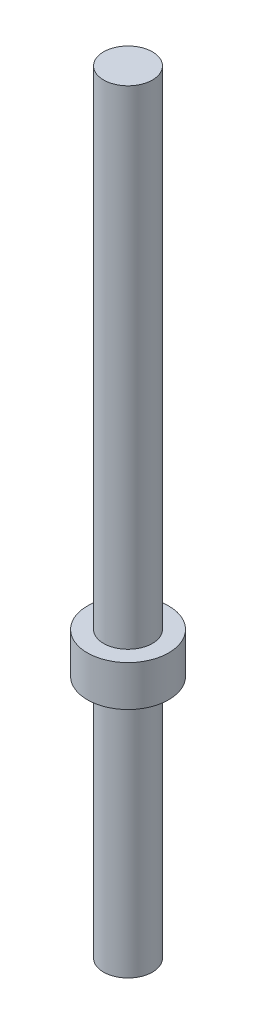
SolidWorks part; units mm, degrees
ref_plane "Front Plane" through (0, 0, 0) normal (0, 0, 1) x (1, 0, 0)
ref_plane "Top Plane" through (0, 0, 0) normal (0, 1, 0) x (1, 0, 0)
ref_plane "Right Plane" through (0, 0, 0) normal (1, 0, 0) x (0, 0, -1)
sketch "Sketch2" plane through (0, 0, 0) normal (0, 1, 0) x (1, 0, 0)
  circle A0 centre (0, 0) radius 0.3
  dimension "D1" = 0.6
extrude "Base-Extrude" add sketch "Sketch2" along normal blind 6.5
sketch "Sketch3" plane through (0, 0, 0) normal (0, -1, 0) x (1, 0, 0)
  circle A0 centre (0, 0) radius 0.5
  circle A1 centre (0, 0) radius 0.3 construction
  dimension "D1" = 1
extrude "Boss-Extrude1" add sketch "Sketch3" against normal blind 0.5
sketch "Sketch4" plane through (0, 0, 0) normal (0, -1, 0) x (1, 0, 0)
  circle A0 centre (0, 0) radius 0.3
  circle A1 centre (0, 0) radius 0.3 construction
extrude "Boss-Extrude2" add sketch "Sketch4" along normal blind 3
ref_plane "Board Plane" through (0, -3, 0) normal (0, 1, 0) x (-1, 0, 0)
sketch "Component_Outline" plane through (0, -3, 0) normal (0, 1, 0) x (-1, 0, 0)
  circle A0 centre (0, 0) radius 0.5
  circle A1 centre (0, 0) radius 0.5 construction
